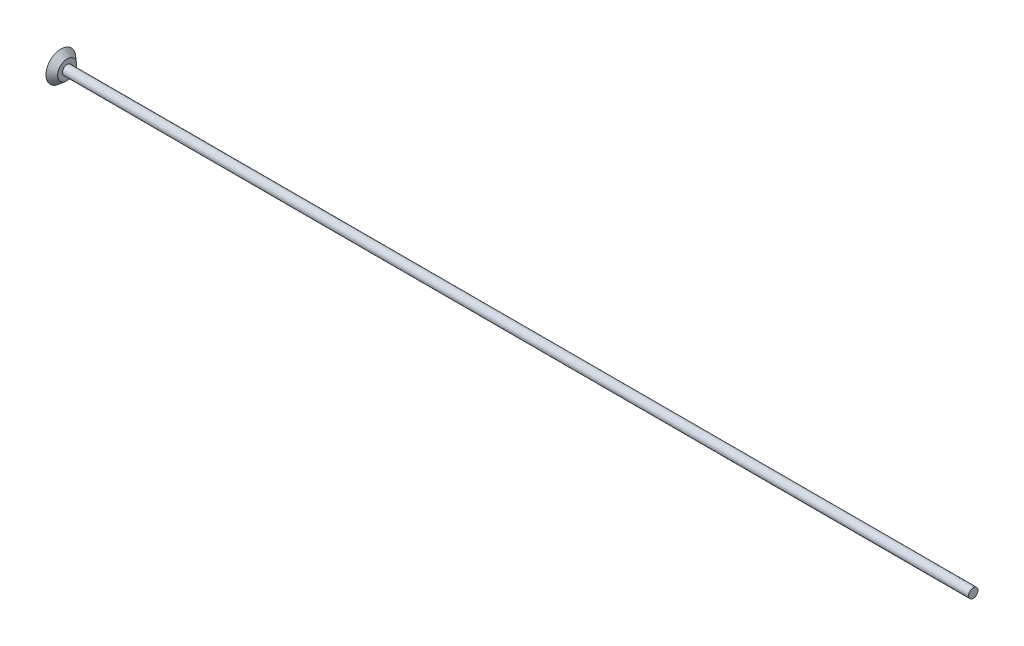
SolidWorks part; units mm, degrees
ref_plane "Front Plane" through (0, 0, 0) normal (0, 0, 1) x (1, 0, 0)
ref_plane "Top Plane" through (0, 0, 0) normal (0, 1, 0) x (1, 0, 0)
ref_plane "Right Plane" through (0, 0, 0) normal (1, 0, 0) x (0, 0, -1)
sketch "Sketch1" plane through (0, 0, 0) normal (0, 1, 0) x (1, 0, 0)
  line L0 (0, 0) -> (0, 4.7625)
  line L1 (0, 4.7625) -> (2, 3.0136)
  line L2 (2, 3.0136) -> (2, 1.5)
  line L3 (2, 1.5) -> (292.0307, 1.5)
  line L4 (292.0307, 1.5) -> (292.0307, 0)
  line L5 (292.0307, 0) -> (0, 0)
  dimension "D1" = 1.5
  dimension "D2" = 4.7625
  dimension "D3" = 2
revolve "Revolve1" add sketch "Sketch1" angle 360 about L5
